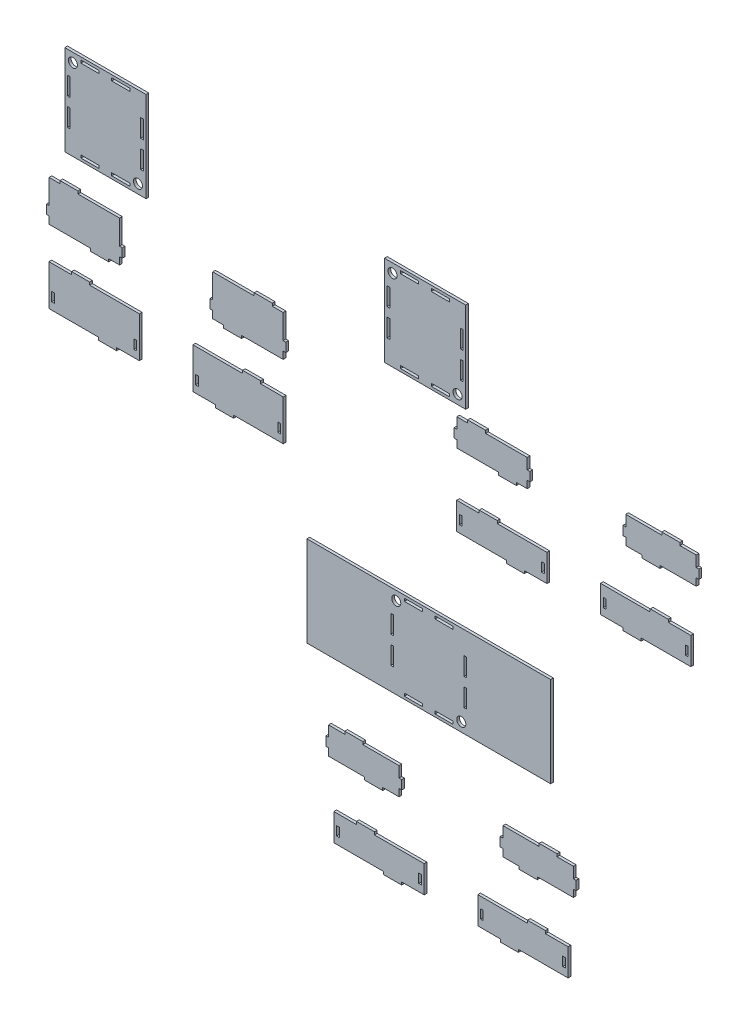
SolidWorks part; units mm, degrees
ref_plane "Спереди" through (0, 0, 0) normal (0, 0, 1) x (1, 0, 0)
ref_plane "Сверху" through (0, 0, 0) normal (0, 1, 0) x (1, 0, 0)
ref_plane "Справа" through (0, 0, 0) normal (1, 0, 0) x (0, 0, -1)
sketch "Эскиз1" plane through (0, 0, 0) normal (0, 0, 1) x (1, 0, 0)
  line L11 (-251.1655, 199.705) -> (-254.1655, 199.705)
  line L32 (-251.1655, 226.705) -> (-239.1655, 226.705)
  line L42 (-196.2718, 100.8335) -> (-196.2718, 97.8335)
  line L43 (-251.2718, 145.8335) -> (-226.2718, 145.8335)
  line L44 (-251.2718, 145.8335) -> (-251.2718, 100.8335)
  line L45 (-251.2718, 100.8335) -> (-196.2718, 100.8335)
  line L46 (-151.2718, 145.8335) -> (-151.2718, 100.8335)
  line L47 (-248.2718, 118.8335) -> (-245.2718, 118.8335)
  line L48 (-248.2718, 118.8335) -> (-248.2718, 108.8335)
  line L49 (-248.2718, 108.8335) -> (-245.2718, 108.8335)
  line L50 (-245.2718, 118.8335) -> (-245.2718, 108.8335)
  line L51 (-157.2718, 118.8335) -> (-154.2718, 118.8335)
  line L52 (-157.2718, 118.8335) -> (-157.2718, 108.8335)
  line L53 (-157.2718, 108.8335) -> (-154.2718, 108.8335)
  line L54 (-154.2718, 118.8335) -> (-154.2718, 108.8335)
  line L55 (-196.2718, 97.8335) -> (-176.2718, 97.8335)
  line L56 (-176.2718, 97.8335) -> (-176.2718, 100.8335)
  line L57 (-226.2718, 145.8335) -> (-226.2718, 148.8335)
  line L58 (-226.2718, 148.8335) -> (-206.2718, 148.8335)
  line L59 (-206.2718, 148.8335) -> (-206.2718, 145.8335)
  line L60 (-176.2718, 100.8335) -> (-151.2718, 100.8335)
  line L61 (-206.2718, 145.8335) -> (-151.2718, 145.8335)
  line L93 (-121.597, -804.4399) -> (-121.597, 49195.5601) construction
  line L114 (-58.0285, 181.705) -> (-70.0285, 181.705)
  line L175 (-70.0285, 189.705) -> (-70.0285, 181.705)
  line L196 (-24.0285, 226.705) -> (-70.0285, 226.705)
  line L247 (-233.8227, 359.8799) -> (-143.8227, 359.8799)
  line L248 (-233.8227, 359.8799) -> (-233.8227, 259.8799)
  line L249 (-233.8227, 259.8799) -> (-143.8227, 259.8799)
  line L250 (-143.8227, 359.8799) -> (-143.8227, 259.8799)
  line L251 (-230.8227, 304.8799) -> (-227.8227, 304.8799)
  line L252 (-230.8227, 304.8799) -> (-230.8227, 284.8799)
  line L253 (-230.8227, 284.8799) -> (-227.8227, 284.8799)
  line L254 (-227.8227, 304.8799) -> (-227.8227, 284.8799)
  line L255 (-215.8227, 356.8799) -> (-195.8227, 356.8799)
  line L256 (-215.8227, 356.8799) -> (-215.8227, 353.8799)
  line L257 (-215.8227, 353.8799) -> (-195.8227, 353.8799)
  line L258 (-195.8227, 356.8799) -> (-195.8227, 353.8799)
  line L259 (-146.8227, 304.8799) -> (-149.8227, 304.8799)
  line L260 (-146.8227, 304.8799) -> (-146.8227, 284.8799)
  line L261 (-146.8227, 284.8799) -> (-149.8227, 284.8799)
  line L262 (-149.8227, 304.8799) -> (-149.8227, 284.8799)
  line L263 (-215.8227, 262.8799) -> (-195.8227, 262.8799)
  line L264 (-215.8227, 262.8799) -> (-215.8227, 265.8799)
  line L265 (-215.8227, 265.8799) -> (-195.8227, 265.8799)
  line L266 (-195.8227, 262.8799) -> (-195.8227, 265.8799)
  line L267 (-181.8227, 353.8799) -> (-161.8227, 353.8799)
  line L268 (-181.8227, 353.8799) -> (-181.8227, 356.8799)
  line L269 (-181.8227, 356.8799) -> (-161.8227, 356.8799)
  line L270 (-161.8227, 353.8799) -> (-161.8227, 356.8799)
  line L271 (-146.8227, 334.8799) -> (-149.8227, 334.8799)
  line L272 (-146.8227, 334.8799) -> (-146.8227, 314.8799)
  line L273 (-146.8227, 314.8799) -> (-149.8227, 314.8799)
  line L274 (-149.8227, 334.8799) -> (-149.8227, 314.8799)
  line L275 (-230.8227, 334.8799) -> (-227.8227, 334.8799)
  line L276 (-230.8227, 334.8799) -> (-230.8227, 314.8799)
  line L277 (-230.8227, 314.8799) -> (-227.8227, 314.8799)
  line L278 (-227.8227, 334.8799) -> (-227.8227, 314.8799)
  line L279 (-181.8227, 265.8799) -> (-161.8227, 265.8799)
  line L280 (-181.8227, 265.8799) -> (-181.8227, 262.8799)
  line L281 (-181.8227, 262.8799) -> (-161.8227, 262.8799)
  line L282 (-161.8227, 265.8799) -> (-161.8227, 262.8799)
  line L318 (-251.1655, 226.705) -> (-251.1655, 199.705)
  line L319 (-251.1655, 181.705) -> (-205.1655, 181.705)
  line L320 (-173.1655, 226.705) -> (-173.1655, 199.705)
  line L321 (-254.1655, 199.705) -> (-254.1655, 189.705)
  line L322 (-254.1655, 189.705) -> (-251.1655, 189.705)
  line L323 (-205.1655, 181.705) -> (-205.1655, 178.705)
  line L324 (-205.1655, 178.705) -> (-185.1655, 178.705)
  line L325 (-185.1655, 178.705) -> (-185.1655, 181.705)
  line L326 (-173.1655, 199.705) -> (-170.1655, 199.705)
  line L327 (-170.1655, 199.705) -> (-170.1655, 189.705)
  line L328 (-170.1655, 189.705) -> (-173.1655, 189.705)
  line L329 (-239.1655, 226.705) -> (-239.1655, 229.705)
  line L330 (-239.1655, 229.705) -> (-219.1655, 229.705)
  line L331 (-219.1655, 229.705) -> (-219.1655, 226.705)
  line L332 (-251.1655, 189.705) -> (-251.1655, 181.705)
  line L333 (-219.1655, 226.705) -> (-173.1655, 226.705)
  line L334 (-173.1655, 189.705) -> (-173.1655, 181.705)
  line L335 (-185.1655, 181.705) -> (-173.1655, 181.705)
  line L336 (7.9715, 189.705) -> (7.9715, 181.705)
  line L337 (-24.0285, 229.705) -> (-24.0285, 226.705)
  line L338 (-4.0285, 229.705) -> (-24.0285, 229.705)
  line L339 (-4.0285, 226.705) -> (-4.0285, 229.705)
  line L340 (-73.0285, 189.705) -> (-70.0285, 189.705)
  line L341 (-73.0285, 199.705) -> (-73.0285, 189.705)
  line L342 (-70.0285, 199.705) -> (-73.0285, 199.705)
  line L343 (-58.0285, 178.705) -> (-58.0285, 181.705)
  line L344 (-38.0285, 178.705) -> (-58.0285, 178.705)
  line L345 (-38.0285, 181.705) -> (-38.0285, 178.705)
  line L346 (10.9715, 189.705) -> (7.9715, 189.705)
  line L347 (10.9715, 199.705) -> (10.9715, 189.705)
  line L348 (-70.0285, 226.705) -> (-70.0285, 199.705)
  line L349 (7.9715, 181.705) -> (-38.0285, 181.705)
  line L350 (7.9715, 226.705) -> (7.9715, 199.705)
  line L351 (-36.9222, 145.8335) -> (-91.9222, 145.8335)
  line L352 (-66.9222, 100.8335) -> (-91.9222, 100.8335)
  line L353 (-36.9222, 148.8335) -> (-36.9222, 145.8335)
  line L354 (-16.9222, 148.8335) -> (-36.9222, 148.8335)
  line L355 (-16.9222, 145.8335) -> (-16.9222, 148.8335)
  line L356 (-66.9222, 97.8335) -> (-66.9222, 100.8335)
  line L357 (-46.9222, 97.8335) -> (-66.9222, 97.8335)
  line L358 (-88.9222, 118.8335) -> (-88.9222, 108.8335)
  line L359 (-85.9222, 108.8335) -> (-88.9222, 108.8335)
  line L360 (-85.9222, 118.8335) -> (-85.9222, 108.8335)
  line L361 (-85.9222, 118.8335) -> (-88.9222, 118.8335)
  line L362 (2.0778, 118.8335) -> (2.0778, 108.8335)
  line L363 (5.0778, 108.8335) -> (2.0778, 108.8335)
  line L364 (5.0778, 118.8335) -> (5.0778, 108.8335)
  line L365 (5.0778, 118.8335) -> (2.0778, 118.8335)
  line L366 (-91.9222, 145.8335) -> (-91.9222, 100.8335)
  line L367 (8.0778, 100.8335) -> (-46.9222, 100.8335)
  line L368 (8.0778, 145.8335) -> (8.0778, 100.8335)
  line L369 (8.0778, 145.8335) -> (-16.9222, 145.8335)
  line L370 (-46.9222, 100.8335) -> (-46.9222, 97.8335)
  line L371 (7.9715, 226.705) -> (-4.0285, 226.705)
  line L372 (7.9715, 199.705) -> (10.9715, 199.705)
  line L398 (120.1372, 334.937) -> (210.1372, 334.937)
  line L399 (120.1372, 334.937) -> (120.1372, 234.937)
  line L400 (120.1372, 234.937) -> (210.1372, 234.937)
  line L401 (210.1372, 334.937) -> (210.1372, 234.937)
  line L402 (123.1372, 279.937) -> (126.1372, 279.937)
  line L403 (123.1372, 279.937) -> (123.1372, 259.937)
  line L404 (123.1372, 259.937) -> (126.1372, 259.937)
  line L405 (126.1372, 279.937) -> (126.1372, 259.937)
  line L406 (138.1372, 331.937) -> (158.1372, 331.937)
  line L407 (138.1372, 331.937) -> (138.1372, 328.937)
  line L408 (138.1372, 328.937) -> (158.1372, 328.937)
  line L409 (158.1372, 331.937) -> (158.1372, 328.937)
  line L410 (207.1372, 279.937) -> (204.1372, 279.937)
  line L411 (207.1372, 279.937) -> (207.1372, 259.937)
  line L412 (207.1372, 259.937) -> (204.1372, 259.937)
  line L413 (204.1372, 279.937) -> (204.1372, 259.937)
  line L414 (138.1372, 237.937) -> (158.1372, 237.937)
  line L415 (138.1372, 237.937) -> (138.1372, 240.937)
  line L416 (138.1372, 240.937) -> (158.1372, 240.937)
  line L417 (158.1372, 237.937) -> (158.1372, 240.937)
  line L418 (172.1372, 328.937) -> (192.1372, 328.937)
  line L419 (172.1372, 328.937) -> (172.1372, 331.937)
  line L420 (172.1372, 331.937) -> (192.1372, 331.937)
  line L421 (192.1372, 328.937) -> (192.1372, 331.937)
  line L422 (207.1372, 309.937) -> (204.1372, 309.937)
  line L423 (207.1372, 309.937) -> (207.1372, 289.937)
  line L424 (207.1372, 289.937) -> (204.1372, 289.937)
  line L425 (204.1372, 309.937) -> (204.1372, 289.937)
  line L426 (123.1372, 309.937) -> (126.1372, 309.937)
  line L427 (123.1372, 309.937) -> (123.1372, 289.937)
  line L428 (123.1372, 289.937) -> (126.1372, 289.937)
  line L429 (126.1372, 309.937) -> (126.1372, 289.937)
  line L430 (172.1372, 240.937) -> (192.1372, 240.937)
  line L431 (172.1372, 240.937) -> (172.1372, 237.937)
  line L432 (172.1372, 237.937) -> (192.1372, 237.937)
  line L433 (192.1372, 240.937) -> (192.1372, 237.937)
  line L514 (124.2667, 22.8612) -> (214.2667, 22.8612)
  line L516 (124.2667, -77.1388) -> (214.2667, -77.1388)
  line L518 (127.2667, -32.1388) -> (130.2667, -32.1388)
  line L519 (127.2667, -32.1388) -> (127.2667, -52.1388)
  line L520 (127.2667, -52.1388) -> (130.2667, -52.1388)
  line L521 (130.2667, -32.1388) -> (130.2667, -52.1388)
  line L522 (142.2667, 19.8612) -> (162.2667, 19.8612)
  line L523 (142.2667, 19.8612) -> (142.2667, 16.8612)
  line L524 (142.2667, 16.8612) -> (162.2667, 16.8612)
  line L525 (162.2667, 19.8612) -> (162.2667, 16.8612)
  line L526 (211.2667, -32.1388) -> (208.2667, -32.1388)
  line L527 (211.2667, -32.1388) -> (211.2667, -52.1388)
  line L528 (211.2667, -52.1388) -> (208.2667, -52.1388)
  line L529 (208.2667, -32.1388) -> (208.2667, -52.1388)
  line L530 (142.2667, -74.1388) -> (162.2667, -74.1388)
  line L531 (142.2667, -74.1388) -> (142.2667, -71.1388)
  line L532 (142.2667, -71.1388) -> (162.2667, -71.1388)
  line L533 (162.2667, -74.1388) -> (162.2667, -71.1388)
  line L534 (176.2667, 16.8612) -> (196.2667, 16.8612)
  line L535 (176.2667, 16.8612) -> (176.2667, 19.8612)
  line L536 (176.2667, 19.8612) -> (196.2667, 19.8612)
  line L537 (196.2667, 16.8612) -> (196.2667, 19.8612)
  line L538 (211.2667, -2.1388) -> (208.2667, -2.1388)
  line L539 (211.2667, -2.1388) -> (211.2667, -22.1388)
  line L540 (211.2667, -22.1388) -> (208.2667, -22.1388)
  line L541 (208.2667, -2.1388) -> (208.2667, -22.1388)
  line L542 (127.2667, -2.1388) -> (130.2667, -2.1388)
  line L543 (127.2667, -2.1388) -> (127.2667, -22.1388)
  line L544 (127.2667, -22.1388) -> (130.2667, -22.1388)
  line L545 (130.2667, -2.1388) -> (130.2667, -22.1388)
  line L546 (176.2667, -71.1388) -> (196.2667, -71.1388)
  line L547 (176.2667, -71.1388) -> (176.2667, -74.1388)
  line L548 (176.2667, -74.1388) -> (196.2667, -74.1388)
  line L549 (196.2667, -71.1388) -> (196.2667, -74.1388)
  line L605 (124.2667, 22.8612) -> (34.2667, 22.8612)
  line L610 (34.2667, 22.8612) -> (34.2667, -77.1388)
  line L611 (34.2667, -77.1388) -> (124.2667, -77.1388)
  line L612 (214.2667, -77.1388) -> (304.2667, -77.1388)
  line L613 (304.2667, -77.1388) -> (304.2667, 22.8612)
  line L614 (304.2667, 22.8612) -> (214.2667, 22.8612)
  line L615 (200.25, 210.8868) -> (197.25, 210.8868)
  line L616 (200.25, 222.8868) -> (212.25, 222.8868)
  line L617 (255.1437, 112.7755) -> (255.1437, 109.7755)
  line L618 (200.1437, 142.7755) -> (225.1437, 142.7755)
  line L619 (200.1437, 142.7755) -> (200.1437, 112.7755)
  line L620 (200.1437, 112.7755) -> (255.1437, 112.7755)
  line L621 (300.1437, 142.7755) -> (300.1437, 112.7755)
  line L622 (203.1437, 130.7755) -> (206.1437, 130.7755)
  line L623 (203.1437, 130.7755) -> (203.1437, 120.7755)
  line L624 (203.1437, 120.7755) -> (206.1437, 120.7755)
  line L625 (206.1437, 130.7755) -> (206.1437, 120.7755)
  line L626 (294.1437, 130.7755) -> (297.1437, 130.7755)
  line L627 (294.1437, 130.7755) -> (294.1437, 120.7755)
  line L628 (294.1437, 120.7755) -> (297.1437, 120.7755)
  line L629 (297.1437, 130.7755) -> (297.1437, 120.7755)
  line L630 (255.1437, 109.7755) -> (275.1437, 109.7755)
  line L631 (275.1437, 109.7755) -> (275.1437, 112.7755)
  line L632 (225.1437, 142.7755) -> (225.1437, 145.7755)
  line L633 (225.1437, 145.7755) -> (245.1437, 145.7755)
  line L634 (245.1437, 145.7755) -> (245.1437, 142.7755)
  line L635 (275.1437, 112.7755) -> (300.1437, 112.7755)
  line L636 (245.1437, 142.7755) -> (300.1437, 142.7755)
  line L637 (405.387, 192.8868) -> (387.387, 192.8868)
  line L638 (387.387, 200.8868) -> (387.387, 192.8868)
  line L639 (427.387, 222.8868) -> (387.387, 222.8868)
  line L640 (200.25, 222.8868) -> (200.25, 210.8868)
  line L641 (200.25, 192.8868) -> (246.25, 192.8868)
  line L642 (278.25, 222.8868) -> (278.25, 210.8868)
  line L643 (197.25, 210.8868) -> (197.25, 200.8868)
  line L644 (197.25, 200.8868) -> (200.25, 200.8868)
  line L645 (246.25, 192.8868) -> (246.25, 189.8868)
  line L646 (246.25, 189.8868) -> (266.25, 189.8868)
  line L647 (266.25, 189.8868) -> (266.25, 192.8868)
  line L648 (278.25, 210.8868) -> (281.25, 210.8868)
  line L649 (281.25, 210.8868) -> (281.25, 200.8868)
  line L650 (281.25, 200.8868) -> (278.25, 200.8868)
  line L651 (212.25, 222.8868) -> (212.25, 225.8868)
  line L652 (212.25, 225.8868) -> (232.25, 225.8868)
  line L653 (232.25, 225.8868) -> (232.25, 222.8868)
  line L654 (200.25, 200.8868) -> (200.25, 192.8868)
  line L655 (232.25, 222.8868) -> (278.25, 222.8868)
  line L656 (278.25, 200.8868) -> (278.25, 192.8868)
  line L657 (266.25, 192.8868) -> (278.25, 192.8868)
  line L658 (465.387, 200.8868) -> (465.387, 192.8868)
  line L659 (427.387, 225.8868) -> (427.387, 222.8868)
  line L660 (447.387, 225.8868) -> (427.387, 225.8868)
  line L661 (447.387, 222.8868) -> (447.387, 225.8868)
  line L662 (384.387, 200.8868) -> (387.387, 200.8868)
  line L663 (384.387, 210.8868) -> (384.387, 200.8868)
  line L664 (387.387, 210.8868) -> (384.387, 210.8868)
  line L665 (405.387, 189.8868) -> (405.387, 192.8868)
  line L666 (425.387, 189.8868) -> (405.387, 189.8868)
  line L667 (425.387, 192.8868) -> (425.387, 189.8868)
  line L668 (468.387, 200.8868) -> (465.387, 200.8868)
  line L669 (468.387, 210.8868) -> (468.387, 200.8868)
  line L670 (387.387, 222.8868) -> (387.387, 210.8868)
  line L671 (465.387, 192.8868) -> (425.387, 192.8868)
  line L672 (465.387, 222.8868) -> (465.387, 210.8868)
  line L673 (414.4934, 142.7755) -> (359.4934, 142.7755)
  line L674 (384.4934, 112.7755) -> (359.4934, 112.7755)
  line L675 (414.4934, 145.7755) -> (414.4934, 142.7755)
  line L676 (434.4934, 145.7755) -> (414.4934, 145.7755)
  line L677 (434.4934, 142.7755) -> (434.4934, 145.7755)
  line L678 (384.4934, 109.7755) -> (384.4934, 112.7755)
  line L679 (404.4934, 109.7755) -> (384.4934, 109.7755)
  line L680 (362.4934, 130.7755) -> (362.4934, 120.7755)
  line L681 (365.4934, 120.7755) -> (362.4934, 120.7755)
  line L682 (365.4934, 130.7755) -> (365.4934, 120.7755)
  line L683 (365.4934, 130.7755) -> (362.4934, 130.7755)
  line L684 (453.4934, 130.7755) -> (453.4934, 120.7755)
  line L685 (456.4934, 120.7755) -> (453.4934, 120.7755)
  line L686 (456.4934, 130.7755) -> (456.4934, 120.7755)
  line L687 (456.4934, 130.7755) -> (453.4934, 130.7755)
  line L688 (359.4934, 142.7755) -> (359.4934, 112.7755)
  line L689 (459.4934, 112.7755) -> (404.4934, 112.7755)
  line L690 (459.4934, 142.7755) -> (459.4934, 112.7755)
  line L691 (459.4934, 142.7755) -> (434.4934, 142.7755)
  line L692 (404.4934, 112.7755) -> (404.4934, 109.7755)
  line L693 (465.387, 222.8868) -> (447.387, 222.8868)
  line L694 (465.387, 210.8868) -> (468.387, 210.8868)
  line L695 (58.2619, -155.6255) -> (55.2619, -155.6255)
  line L696 (58.2619, -143.6255) -> (76.2619, -143.6255)
  line L697 (119.1556, -253.7368) -> (119.1556, -256.7368)
  line L698 (64.1556, -223.7368) -> (89.1556, -223.7368)
  line L699 (64.1556, -223.7368) -> (64.1556, -253.7368)
  line L700 (64.1556, -253.7368) -> (119.1556, -253.7368)
  line L701 (164.1556, -223.7368) -> (164.1556, -253.7368)
  line L702 (67.1556, -235.7368) -> (70.1556, -235.7368)
  line L703 (67.1556, -235.7368) -> (67.1556, -245.7368)
  line L704 (67.1556, -245.7368) -> (70.1556, -245.7368)
  line L705 (70.1556, -235.7368) -> (70.1556, -245.7368)
  line L706 (158.1556, -235.7368) -> (161.1556, -235.7368)
  line L707 (158.1556, -235.7368) -> (158.1556, -245.7368)
  line L708 (158.1556, -245.7368) -> (161.1556, -245.7368)
  line L709 (161.1556, -235.7368) -> (161.1556, -245.7368)
  line L710 (119.1556, -256.7368) -> (139.1556, -256.7368)
  line L711 (139.1556, -256.7368) -> (139.1556, -253.7368)
  line L712 (89.1556, -223.7368) -> (89.1556, -220.7368)
  line L713 (89.1556, -220.7368) -> (109.1556, -220.7368)
  line L714 (109.1556, -220.7368) -> (109.1556, -223.7368)
  line L715 (139.1556, -253.7368) -> (164.1556, -253.7368)
  line L716 (109.1556, -223.7368) -> (164.1556, -223.7368)
  line L717 (269.3989, -173.6255) -> (251.3989, -173.6255)
  line L718 (251.3989, -165.6255) -> (251.3989, -173.6255)
  line L719 (291.3989, -143.6255) -> (251.3989, -143.6255)
  line L720 (58.2619, -143.6255) -> (58.2619, -155.6255)
  line L721 (58.2619, -173.6255) -> (98.2619, -173.6255)
  line L722 (136.2619, -143.6255) -> (136.2619, -155.6255)
  line L723 (55.2619, -155.6255) -> (55.2619, -165.6255)
  line L724 (55.2619, -165.6255) -> (58.2619, -165.6255)
  line L725 (98.2619, -173.6255) -> (98.2619, -176.6255)
  line L726 (98.2619, -176.6255) -> (118.2619, -176.6255)
  line L727 (118.2619, -176.6255) -> (118.2619, -173.6255)
  line L728 (136.2619, -155.6255) -> (139.2619, -155.6255)
  line L729 (139.2619, -155.6255) -> (139.2619, -165.6255)
  line L730 (139.2619, -165.6255) -> (136.2619, -165.6255)
  line L731 (76.2619, -143.6255) -> (76.2619, -140.6255)
  line L732 (76.2619, -140.6255) -> (96.2619, -140.6255)
  line L733 (96.2619, -140.6255) -> (96.2619, -143.6255)
  line L734 (58.2619, -165.6255) -> (58.2619, -173.6255)
  line L735 (96.2619, -143.6255) -> (136.2619, -143.6255)
  line L736 (136.2619, -165.6255) -> (136.2619, -173.6255)
  line L737 (118.2619, -173.6255) -> (136.2619, -173.6255)
  line L738 (329.3989, -165.6255) -> (329.3989, -173.6255)
  line L739 (291.3989, -140.6255) -> (291.3989, -143.6255)
  line L740 (311.3989, -140.6255) -> (291.3989, -140.6255)
  line L741 (311.3989, -143.6255) -> (311.3989, -140.6255)
  line L742 (248.3989, -165.6255) -> (251.3989, -165.6255)
  line L743 (248.3989, -155.6255) -> (248.3989, -165.6255)
  line L744 (251.3989, -155.6255) -> (248.3989, -155.6255)
  line L745 (269.3989, -176.6255) -> (269.3989, -173.6255)
  line L746 (289.3989, -176.6255) -> (269.3989, -176.6255)
  line L747 (289.3989, -173.6255) -> (289.3989, -176.6255)
  line L748 (332.3989, -165.6255) -> (329.3989, -165.6255)
  line L749 (332.3989, -155.6255) -> (332.3989, -165.6255)
  line L750 (251.3989, -143.6255) -> (251.3989, -155.6255)
  line L751 (329.3989, -173.6255) -> (289.3989, -173.6255)
  line L752 (329.3989, -143.6255) -> (329.3989, -155.6255)
  line L753 (278.5052, -223.7368) -> (223.5052, -223.7368)
  line L754 (248.5052, -253.7368) -> (223.5052, -253.7368)
  line L755 (278.5052, -220.7368) -> (278.5052, -223.7368)
  line L756 (298.5052, -220.7368) -> (278.5052, -220.7368)
  line L757 (298.5052, -223.7368) -> (298.5052, -220.7368)
  line L758 (248.5052, -256.7368) -> (248.5052, -253.7368)
  line L759 (268.5052, -256.7368) -> (248.5052, -256.7368)
  line L760 (226.5052, -235.7368) -> (226.5052, -245.7368)
  line L761 (229.5052, -245.7368) -> (226.5052, -245.7368)
  line L762 (229.5052, -235.7368) -> (229.5052, -245.7368)
  line L763 (229.5052, -235.7368) -> (226.5052, -235.7368)
  line L764 (317.5052, -235.7368) -> (317.5052, -245.7368)
  line L765 (320.5052, -245.7368) -> (317.5052, -245.7368)
  line L766 (320.5052, -235.7368) -> (320.5052, -245.7368)
  line L767 (320.5052, -235.7368) -> (317.5052, -235.7368)
  line L768 (223.5052, -223.7368) -> (223.5052, -253.7368)
  line L769 (323.5052, -253.7368) -> (268.5052, -253.7368)
  line L770 (323.5052, -223.7368) -> (323.5052, -253.7368)
  line L771 (323.5052, -223.7368) -> (298.5052, -223.7368)
  line L772 (268.5052, -253.7368) -> (268.5052, -256.7368)
  line L773 (329.3989, -143.6255) -> (311.3989, -143.6255)
  line L774 (329.3989, -155.6255) -> (332.3989, -155.6255)
  circle A1 centre (-152.8227, 269.8799) radius 5
  circle A2 centre (-224.8227, 349.8799) radius 5
  circle A6 centre (201.1372, 244.937) radius 5
  circle A7 centre (129.1372, 324.937) radius 5
  circle A8 centre (205.2667, -67.1388) radius 5
  circle A9 centre (133.2667, 12.8612) radius 5
  dimension "D164" = 10
  dimension "D165" = 10
  dimension "D75" = 10
  dimension "D76" = 10
  dimension "D177" = 10
  dimension "D178" = 10
  dimension "D5" = 8
  dimension "D6" = 3
  dimension "D7" = 3
  dimension "D8" = 8
  dimension "D9" = 8
  dimension "D10" = 20
  dimension "D11" = 3
  dimension "D12" = 20
  dimension "D20" = 100
  dimension "D21" = 8
  dimension "D22" = 3
  dimension "D23" = 3
  dimension "D24" = 10
  dimension "D25" = 10
  dimension "D26" = 3
  dimension "D27" = 3
  dimension "D28" = 3
  dimension "D29" = 20
  dimension "D30" = 25
  dimension "D31" = 25
  dimension "D32" = 78
  dimension "D33" = 3
  dimension "D34" = 45
  dimension "D35" = 3
  dimension "D36" = 10
  dimension "D37" = 10
  dimension "D38" = 3
  dimension "D39" = 3
  dimension "D40" = 20
  dimension "D41" = 25
  dimension "D42" = 3
  dimension "D43" = 30
  dimension "D44" = 3
  dimension "D45" = 78
  dimension "D46" = 30
  dimension "D47" = 90
  dimension "D48" = 3
  dimension "D49" = 12
  dimension "D50" = 25
  dimension "D51" = 25
  dimension "D52" = 20
  dimension "D53" = 100
  dimension "D54" = 25
  dimension "D55" = 3
  dimension "D56" = 10
  dimension "D57" = 20
  dimension "D58" = 20
  dimension "D59" = 3
  dimension "D60" = 3
  dimension "D61" = 20
  dimension "D62" = 3
  dimension "D63" = 3
  dimension "D64" = 3
  dimension "D65" = 20
  dimension "D66" = 3
  dimension "D67" = 20
  dimension "D68" = 20
  dimension "D69" = 20
  dimension "D70" = 3
  dimension "D71" = 3
  dimension "D72" = 3
  dimension "D73" = 9
  dimension "D74" = 10
  dimension "D77" = 9
  dimension "D78" = 10
  dimension "D79" = 20
  dimension "D80" = 3
  dimension "D81" = 3
  dimension "D82" = 18
  dimension "D83" = 3
  dimension "D84" = 18
  dimension "D85" = 10
  dimension "D86" = 18
  dimension "D87" = 3
  dimension "D88" = 25
  dimension "D89" = 3
  dimension "D90" = 8
  dimension "D91" = 3
  dimension "D92" = 3
  dimension "D93" = 8
  dimension "D94" = 20
  dimension "D95" = 3
  dimension "D96" = 20
  dimension "D97" = 3
  dimension "D98" = 12
  dimension "D99" = 20
  dimension "D100" = 12
  dimension "D101" = 25
  dimension "D102" = 8
  dimension "D103" = 3
  dimension "D104" = 25
  dimension "D105" = 25
  dimension "D106" = 10
  dimension "D107" = 10
  dimension "D108" = 3
  dimension "D109" = 3
  dimension "D110" = 20
  dimension "D111" = 25
  dimension "D112" = 3
  dimension "D113" = 30
  dimension "D114" = 3
  dimension "D115" = 78
  dimension "D116" = 30
  dimension "D117" = 10
  dimension "D118" = 10
  dimension "D119" = 8
  dimension "D120" = 3
  dimension "D121" = 12
  dimension "D122" = 100
  dimension "D123" = 25
  dimension "D124" = 3
  dimension "D125" = 3
  dimension "D126" = 20
  dimension "D127" = 20
  dimension "D128" = 3
  dimension "D129" = 8
  dimension "D130" = 20
  dimension "D131" = 3
  dimension "D132" = 3
  dimension "D133" = 3
  dimension "D134" = 20
  dimension "D135" = 20
  dimension "D136" = 90
  dimension "D137" = 100
  dimension "D138" = 25
  dimension "D139" = 3
  dimension "D140" = 18
  dimension "D141" = 20
  dimension "D142" = 20
  dimension "D143" = 3
  dimension "D144" = 3
  dimension "D145" = 20
  dimension "D146" = 20
  dimension "D147" = 3
  dimension "D148" = 18
  dimension "D149" = 3
  dimension "D150" = 3
  dimension "D151" = 20
  dimension "D152" = 3
  dimension "D153" = 20
  dimension "D154" = 20
  dimension "D155" = 20
  dimension "D156" = 3
  dimension "D157" = 3
  dimension "D158" = 3
  dimension "D159" = 3
  dimension "D160" = 3
  dimension "D161" = 18
  dimension "D162" = 9
  dimension "D163" = 10
  dimension "D166" = 9
  dimension "D167" = 10
  dimension "D168" = 20
  dimension "D169" = 20
  dimension "D170" = 3
  dimension "D171" = 20
  dimension "D172" = 3
  dimension "D173" = 3
  dimension "D174" = 3
  dimension "D175" = 3
  dimension "D176" = 10
  dimension "D179" = 20
  dimension "D180" = 10
  dimension "D181" = 20
  dimension "D182" = 3
  dimension "D183" = 3
  dimension "D184" = 3
  dimension "D185" = 3
  dimension "D186" = 18
  dimension "D187" = 20
  dimension "D188" = 18
  dimension "D189" = 3
  dimension "D190" = 25
  dimension "D191" = 25
  dimension "D192" = 8
  dimension "D203" = 3
  dimension "D204" = 18
  dimension "D205" = 3
  dimension "D206" = 25
  dimension "D207" = 3
  dimension "D208" = 45
  dimension "D209" = 10
  dimension "D210" = 10
  dimension "D214" = 25
  dimension "D215" = 25
  dimension "D217" = 90
  dimension "D218" = 90
extrude "Бобышка-Вытянуть1" add sketch "Эскиз1" along normal blind 3
